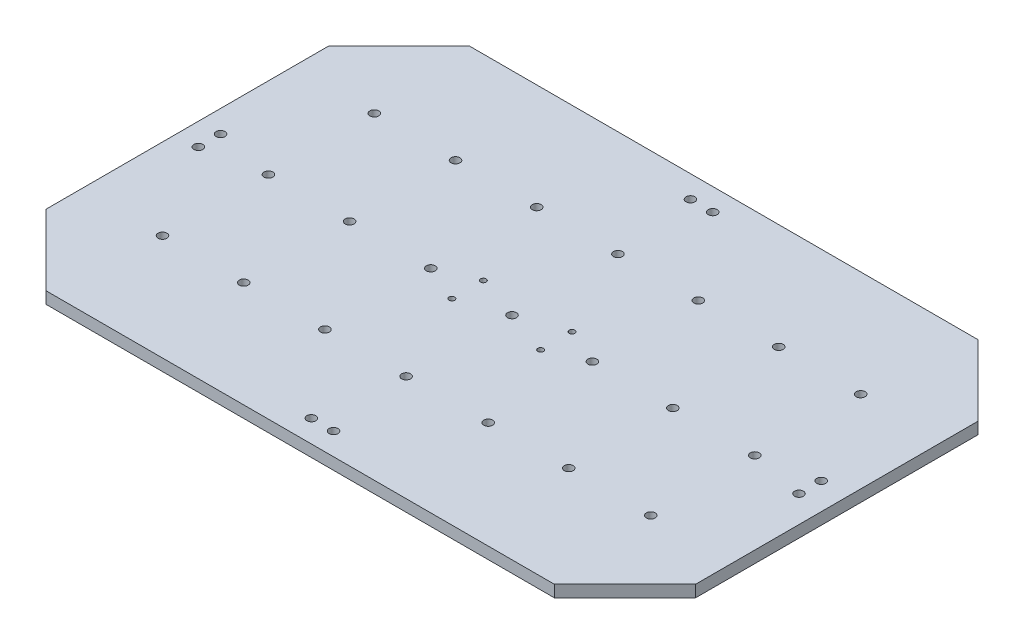
SolidWorks part; units mm, degrees
ref_plane "Front Plane" through (0, 0, 0) normal (0, 0, 1) x (1, 0, 0)
ref_plane "Top Plane" through (0, 0, 0) normal (0, 1, 0) x (1, 0, 0)
ref_plane "Right Plane" through (0, 0, 0) normal (1, 0, 0) x (0, 0, -1)
sketch "Sketch1" plane through (0, 0, 0) normal (0, 1, 0) x (1, 0, 0)
  line L0 (146.05, 0) -> (171.45, 0) construction
  line L1 (-146.05, -95.25) -> (146.05, -95.25)
  line L3 (-146.05, 95.25) -> (146.05, 95.25)
  line L5 (-146.05, -95.25) -> (146.05, 95.25) construction
  line L6 (-146.05, 95.25) -> (146.05, -95.25) construction
  line L7 (-116.8767, 0) -> (-142.2767, 0) construction
  line L11 (146.05, 12.7) -> (146.05, 95.25)
  line L13 (146.05, -12.7) -> (146.05, -95.25)
  line L18 (-146.05, -12.7) -> (-146.05, -95.25)
  line L19 (-146.05, 12.7) -> (-146.05, 95.25)
  line L20 (-146.05, 12.7) -> (-146.05, -12.7)
  line L21 (146.05, -12.7) -> (146.05, 12.7)
  point P0 (0, 0)
  dimension "D1" = 292.1
  dimension "D2" = 190.5
  dimension "D3" = 25.4
  dimension "D6" = 25.4
extrude "Main Plate" add sketch "Sketch1" along normal blind 5.3
sketch "Sketch2" plane through (0, 5.3, 0) normal (0, 1, 0) x (1, 0, 0)
  line L0 (0, 0) -> (0, -95.25) construction
  line L1 (-73.025, 47.625) -> (0, 47.625) construction
  line L2 (0, 47.625) -> (72.3084, 47.625) construction
  line L3 (-146.05, -95.25) -> (146.05, -95.25) construction
  line L4 (72.3084, 47.625) -> (146.05, 47.625) construction
  line L5 (146.05, -95.25) -> (146.05, 95.25) construction
  line L6 (-73.025, -47.625) -> (0, -47.625) construction
  line L7 (0, 0) -> (0, 95.25) construction
  line L8 (0, -47.625) -> (72.3084, -46.7808) construction
  line L9 (72.3084, -46.7808) -> (146.05, -46.7808) construction
  line L10 (-146.05, 0) -> (0, 0) construction
  line L11 (146.05, -95.25) -> (146.05, 95.25) construction
  line L12 (-73.025, 47.625) -> (-146.05, 47.625) construction
  line L13 (146.05, 95.25) -> (-146.05, 95.25) construction
  line L14 (0, 0) -> (144.6168, 0) construction
  line L15 (-146.05, 95.25) -> (-146.05, -95.25) construction
  line L16 (-73.025, 0) -> (-73.025, -95.25) construction
  line L17 (-73.025, 0) -> (-73.025, 95.25) construction
  line L18 (72.3084, 0) -> (72.3084, 95.25) construction
  line L19 (72.3084, 1.6883) -> (72.3084, -95.25) construction
  line L20 (-73.025, -47.625) -> (-146.05, -47.625) construction
  line L21 (-146.05, 95.25) -> (-146.05, -95.25) construction
  line L22 (109.1792, 47.625) -> (109.1792, 0) construction
  line L23 (109.1792, 0) -> (109.1792, -46.7808) construction
  line L24 (109.1792, -46.7808) -> (109.1792, -95.25) construction
  line L25 (36.1542, 47.625) -> (36.1542, 0) construction
  line L26 (36.1542, 0) -> (36.5125, -47.2029) construction
  line L27 (36.5125, -47.2029) -> (36.5125, -95.25) construction
  line L28 (-36.5125, 47.625) -> (-36.5125, 0) construction
  line L29 (-36.5125, 0) -> (-36.5125, -47.625) construction
  line L30 (-36.5125, -47.625) -> (-36.5125, -95.25) construction
  line L31 (-109.5375, 95.25) -> (-109.5375, 47.625) construction
  line L32 (-109.5375, 47.625) -> (-109.5375, 0) construction
  line L33 (-109.5375, 0) -> (-109.5375, -47.625) construction
  line L34 (-109.5375, -47.625) -> (-109.5375, -95.25) construction
  line L35 (-36.5125, 47.625) -> (-36.5125, 95.25) construction
  line L36 (36.1542, 47.625) -> (36.5125, 95.25) construction
  line L37 (109.1792, 47.625) -> (109.1792, 95.25) construction
  circle A0 centre (109.1792, -46.7808) radius 3.47
  circle A1 centre (72.3084, -46.7808) radius 3.7362
hole_wizard "Ø4.0mm Clearance Dowel Hole1" positions "Sketch3" profile "Sketch4" hole size "Ø4.0" standard "ANSI Metric" end condition through all
sketch "Sketch3" plane through (0, 5.3, 0) normal (0, 1, 0) x (1, 0, 0)
  point P0 (109.1792, -46.7808)
  point P3 (72.3084, -46.7808)
  point P6 (36.5125, -47.2029)
  point P9 (109.1792, 0)
  point P12 (72.3084, 0)
  point P15 (36.1542, 0)
  point P18 (109.1792, 47.625)
  point P21 (72.3084, 47.625)
  point P24 (36.1542, 47.625)
  point P27 (0, 47.625)
  point P30 (-36.5125, 47.625)
  point P33 (-73.025, 47.625)
  point P36 (-109.5375, 47.625)
  point P39 (-109.5375, 0)
  point P42 (-73.025, 0)
  point P45 (-36.5125, 0)
  point P47 (0, 0)
  point P50 (0, -47.625)
  point P53 (-36.5125, -47.625)
  point P56 (-73.025, -47.625)
  point P59 (-109.5375, -47.625)
sketch "Sketch4" plane through (109.1792, 5.3, 46.7808) normal (1, 0, 0) x (0, 0, 1)
  line L0 (0, 0) -> (0, 5.3)
  line L1 (0, 5.3) -> (2, 5.3)
  line L2 (2, 5.3) -> (2, 0)
  line L5 (2, 0) -> (0, 0)
  line L11 (0, -6.35) -> (0, 107.95) construction
  dimension "Thru Hole Dia." = 4
  dimension "Thru Hole Depth" = 5.3
sketch "Sketch6" plane through (0, 5.3, 0) normal (0, 1, 0) x (1, 0, 0)
  line L0 (0, -85.25) -> (5, -85.25)
  line L1 (0, -85.25) -> (-5, -85.25)
  line L2 (0, 0) -> (0, -95.25) construction
  line L3 (-146.05, -95.25) -> (146.05, -95.25) construction
  line L4 (0, 85.25) -> (5, 85.25)
  line L5 (0, 85.25) -> (-5, 85.25)
  line L6 (146.05, 95.25) -> (-146.05, 95.25) construction
  line L7 (0, 0) -> (0, 95.25) construction
  line L8 (-136.05, 5) -> (-136.05, 0)
  line L9 (-136.05, 0) -> (-136.05, -5)
  line L10 (-146.05, 95.25) -> (-146.05, -95.25) construction
  dimension "D1" = 5
  dimension "D2" = 5
  dimension "D3" = 0
  dimension "D4" = 10
  dimension "D5" = 10
  dimension "D6" = 5
  dimension "D7" = 5
  dimension "D8" = 0
  dimension "D9" = 10
  dimension "D10" = 5
  dimension "D11" = 5
hole_wizard "Ø4.0mm Clearance Dowel Hole2" positions "Sketch7" profile "Sketch9" hole size "Ø4.0" standard "ANSI Metric" end condition through all
sketch "Sketch7" plane through (0, 5.3, 0) normal (0, 1, 0) x (1, 0, 0)
  line L0 (146.05, -95.25) -> (146.05, 95.25) construction
  line L3 (0, 0) -> (144.6168, 0) construction
  point P0 (5, -85.25)
  point P3 (-5, -85.25)
  point P6 (-136.05, -5)
  point P9 (-136.05, 5)
  point P12 (5, 85.25)
  point P15 (-5, 85.25)
  point P18 (134.05, -5)
  point P20 (134.05, 5)
  dimension "D1" = 12
  dimension "D2" = 12
  dimension "D3" = 5
  dimension "D4" = 5
sketch "Sketch9" plane through (5, 5.3, 85.25) normal (1, 0, 0) x (0, 0, 1)
  line L0 (0, 0) -> (0, 5.3)
  line L1 (0, 5.3) -> (2, 5.3)
  line L2 (2, 5.3) -> (2, 0)
  line L5 (2, 0) -> (0, 0)
  line L11 (0, -6.35) -> (0, 107.95) construction
  dimension "Thru Hole Dia." = 4
  dimension "Thru Hole Depth" = 5.3
hole_wizard "Ø3.0mm Press Dowel Hole1" positions "Sketch10" profile "Sketch11" hole size "Ø3.0" standard "DIN" end condition through all
sketch "Sketch10" plane through (0, 5.3, 0) normal (0, 1, 0) x (1, 0, 0)
  line L0 (-19.96, 7.07) -> (-19.96, -7.07)
  line L2 (-146.05, 0) -> (0, 0) construction
  line L4 (19.96, -7.07) -> (-19.96, -7.07)
  line L7 (-19.96, 7.07) -> (19.96, 7.07)
  line L9 (19.96, 7.07) -> (19.96, -7.07)
  circle A0 centre (0, 0) radius 2 construction
  point P0 (-19.96, 7.07)
  point P2 (-19.96, -7.07)
  point P8 (-19.96, 0)
  point P11 (19.96, 7.07)
  point P12 (19.96, -7.07)
  point P37 (0, -7.07)
  dimension "D1" = 0
  dimension "D2" = 14.14
  dimension "D3" = 39.92
  dimension "D4" = 0
sketch "Sketch11" plane through (-19.96, 5.3, -7.07) normal (1, 0, 0) x (0, 0, 1)
  line L0 (0, 0) -> (0, 5.3)
  line L1 (0, 5.3) -> (1.27, 5.3)
  line L2 (1.27, 5.3) -> (1.27, 0)
  line L5 (1.27, 0) -> (0, 0)
  line L11 (0, -6.35) -> (0, 107.95) construction
  dimension "Thru Hole Dia." = 2.54
  dimension "Thru Hole Depth" = 5.3
sketch "Sketch12" plane through (0, 5.3, 0) normal (0, 1, 0) x (1, 0, 0)
  line L0 (-146.05, 63.5) -> (-114.3, 95.25)
  line L1 (-146.05, 95.25) -> (-146.05, -95.25) construction
  line L2 (146.05, 95.25) -> (-146.05, 95.25) construction
  line L3 (-114.3, 95.25) -> (-146.05, 95.25)
  line L4 (-146.05, 95.25) -> (-146.05, 63.5)
  line L5 (-146.05, -63.5) -> (-114.3, -95.25)
  line L6 (-146.05, -95.25) -> (146.05, -95.25) construction
  line L7 (-114.3, -95.25) -> (-146.05, -95.25)
  line L8 (-146.05, -95.25) -> (-146.05, -63.5)
  line L9 (-146.05, -63.5) -> (-146.05, 63.5)
  line L10 (-146.05, 0) -> (0, 0) construction
  line L11 (146.05, 63.5) -> (114.3, 95.25)
  line L12 (146.05, -95.25) -> (146.05, 95.25) construction
  line L13 (146.05, -63.5) -> (114.3, -95.25)
  line L14 (146.05, 63.5) -> (146.05, 95.25)
  line L15 (146.05, 95.25) -> (114.3, 95.25)
  line L16 (146.05, -63.5) -> (146.05, -95.25)
  line L17 (146.05, -95.25) -> (114.3, -95.25)
  point P16 (-146.05, 0)
  point P23 (146.05, -48.0883)
  line M41 (146.05, -95.25) -> (146.05, 95.25)
  line M42 (146.05, 95.25) -> (-146.05, 95.25)
  line M43 (-146.05, 95.25) -> (-146.05, -95.25)
  line M44 (-146.05, -95.25) -> (146.05, -95.25)
  dimension "D1" = 127
  dimension "D2" = 0
  dimension "D3" = 45
  dimension "D4" = 45
  dimension "D5" = 45
  dimension "D6" = 45
  dimension "D7" = 0
  dimension "D8" = 0
extrude "Cut-Extrude1" cut sketch "Sketch12" against normal through all contours L13 M41 M44 | L5 M43 M44 | L0 M43 M42 | L11 M41 M42
